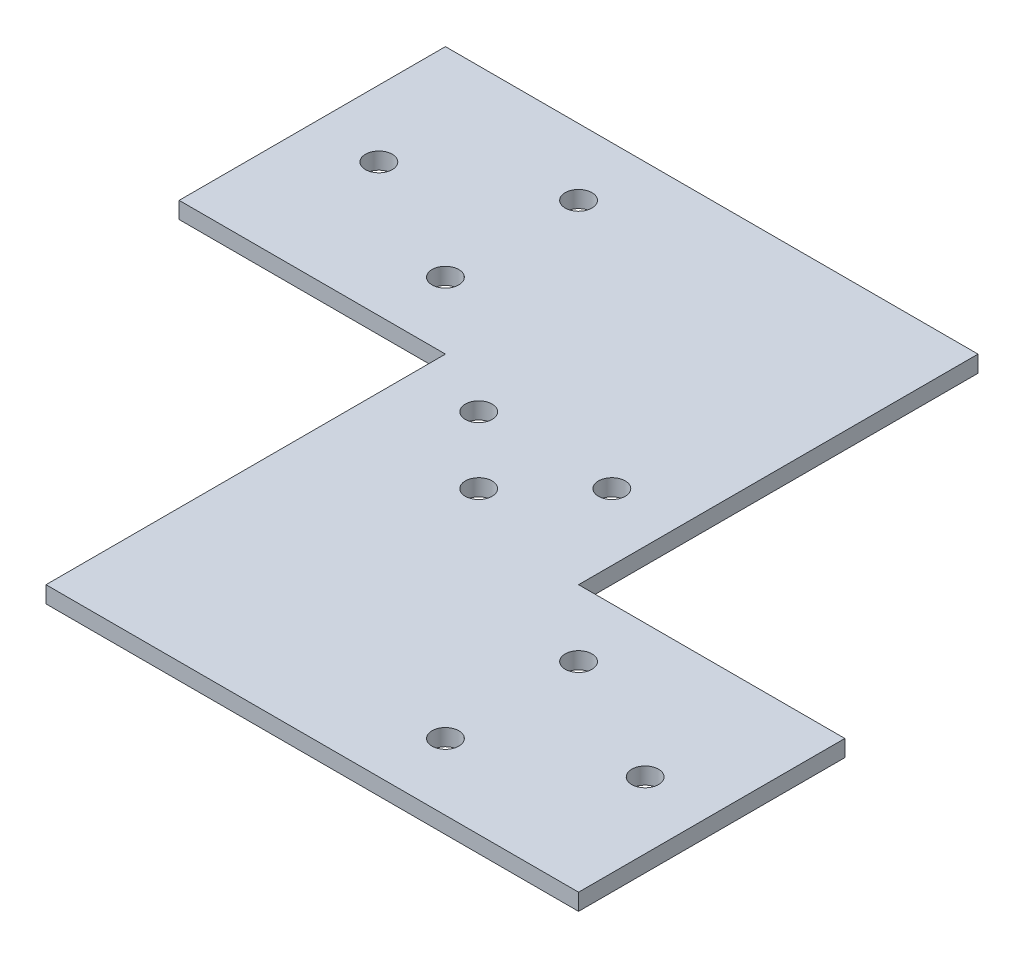
SolidWorks part; units mm, degrees
ref_plane "Front Plane" through (0, 0, 0) normal (0, 0, 1) x (1, 0, 0)
ref_plane "Top Plane" through (0, 0, 0) normal (0, 1, 0) x (1, 0, 0)
ref_plane "Right Plane" through (0, 0, 0) normal (1, 0, 0) x (0, 0, -1)
sketch "Sketch1" plane through (0, 0, 0) normal (0, 1, 0) x (1, 0, 0)
  line L0 (114.3, -38.1) -> (114.3, -63.5) construction
  line L1 (0, 0) -> (50.8, 0)
  line L2 (0, 0) -> (0, 50.8)
  line L3 (0, 50.8) -> (101.6, 50.8)
  line L6 (50.8, 0) -> (50.8, -76.2)
  line L7 (50.8, -76.2) -> (101.6, -76.2)
  line L8 (101.6, 50.8) -> (101.6, -25.4)
  line L9 (101.6, -76.2) -> (152.4, -76.2)
  line L10 (38.1, 38.1) -> (38.1, 12.7) construction
  line L11 (101.6, -25.4) -> (152.4, -25.4)
  line L12 (152.4, -76.2) -> (152.4, -25.4)
  circle A0 centre (12.7, 25.4) radius 2.5527
  circle A1 centre (38.1, 12.7) radius 2.5527
  circle A2 centre (38.1, 38.1) radius 2.5527
  circle A3 centre (139.7, -50.8) radius 2.5527
  circle A4 centre (114.3, -38.1) radius 2.5527
  circle A5 centre (114.3, -63.5) radius 2.5527
  circle A6 centre (63.5, -6.35) radius 2.5527
  circle A7 centre (88.9, -6.35) radius 2.5527
  circle A8 centre (76.2, -19.05) radius 2.5527
  point P23 (0, 25.4)
  point P24 (152.4, -50.8)
  point P25 (114.3, -50.8)
  point P26 (38.1, 25.4)
  dimension "D5" = 5.1054
  dimension "D17" = 5.1054
  dimension "D18" = 12.7
  dimension "D2" = 50.8
  dimension "D3" = 50.8
  dimension "D4" = 50.8
  dimension "D6" = 12.7
  dimension "D7" = 25.4
  dimension "D8" = 25.4
  dimension "D9" = 38.1
  dimension "D10" = 38.1
  dimension "D11" = 50.8
  dimension "D12" = 50.8
  dimension "D13" = 127
  dimension "D14" = 12.7
  dimension "D15" = 57.15
  dimension "D16" = 69.85
  dimension "D19" = 25.4
  dimension "D20" = 38.1
extrude "Boss-Extrude1" add sketch "Sketch1" along normal blind 3.175
